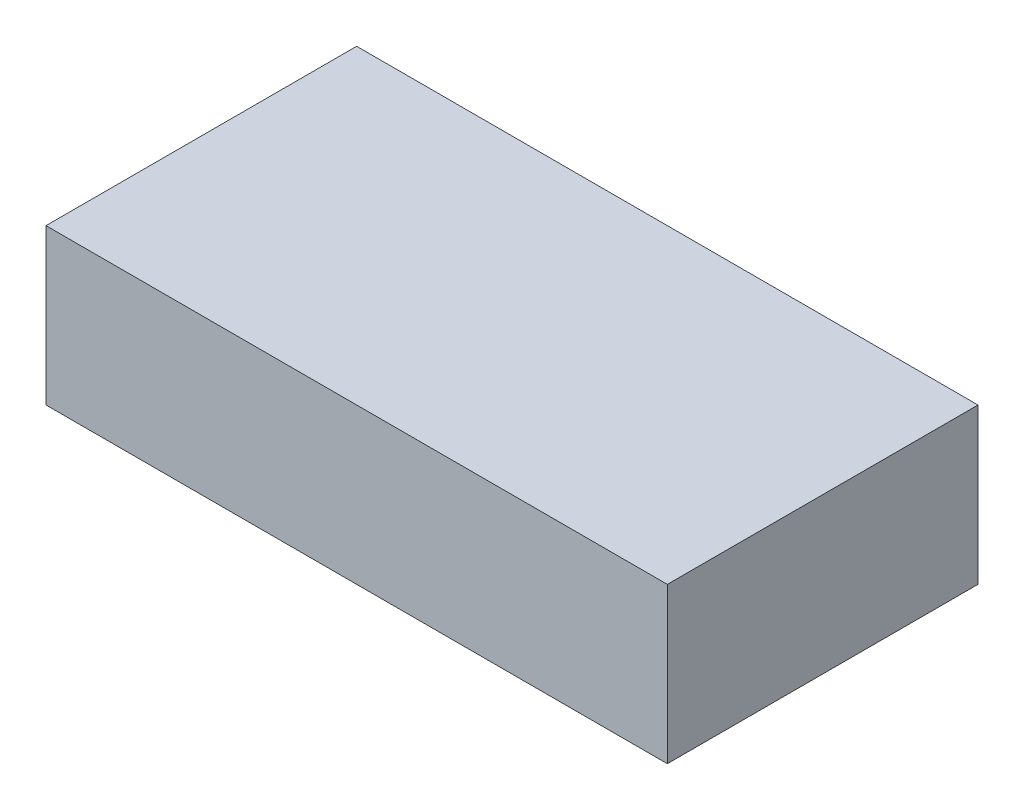
SolidWorks part; units mm, degrees
ref_plane "Front Plane" through (0, 0, 0) normal (0, 0, 1) x (1, 0, 0)
ref_plane "Top Plane" through (0, 0, 0) normal (0, 1, 0) x (1, 0, 0)
ref_plane "Right Plane" through (0, 0, 0) normal (1, 0, 0) x (0, 0, -1)
sketch "Sketch1" plane through (0, 0, 0) normal (0, 1, 0) x (1, 0, 0)
  line L1 (0, 2) -> (4, 2)
  line L2 (0, 2) -> (0, 0)
  line L3 (0, 0) -> (4, 0)
  line L4 (4, 2) -> (4, 0)
  dimension "D1" = 4
  dimension "D2" = 2
extrude "Boss-Extrude1" add sketch "Sketch1" along normal blind 1
